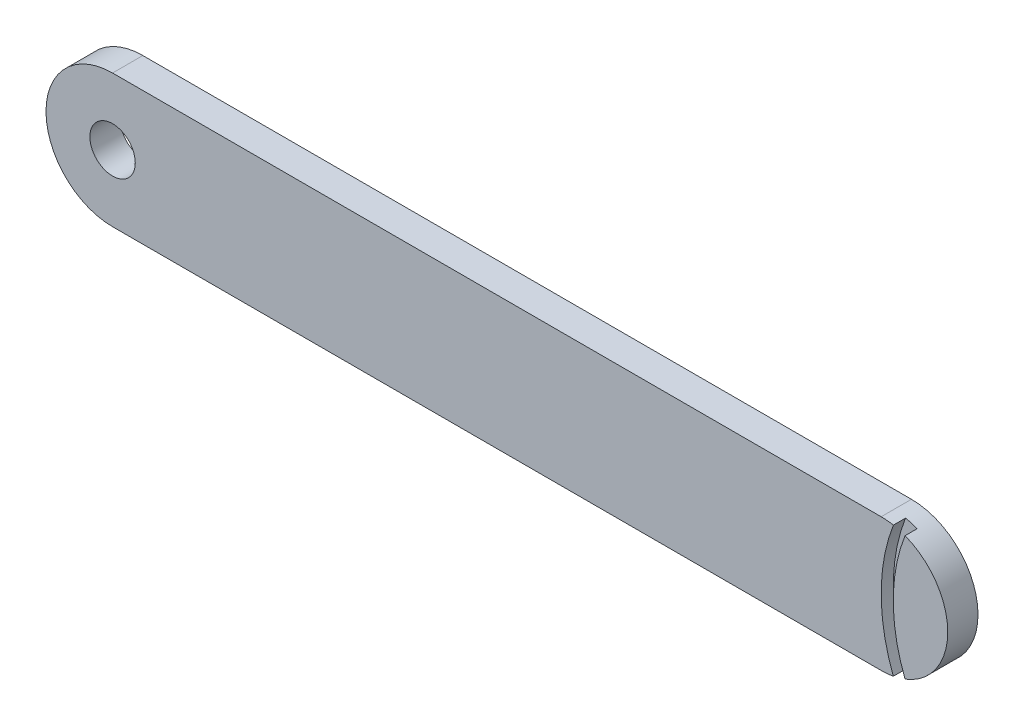
SolidWorks part; units mm, degrees
material "ABS"
ref_plane "Front Plane" through (0, 0, 0) normal (0, 0, 1) x (1, 0, 0)
ref_plane "Top Plane" through (0, 0, 0) normal (0, 1, 0) x (1, 0, 0)
ref_plane "Right Plane" through (0, 0, 0) normal (1, 0, 0) x (0, 0, -1)
sketch "Sketch1" plane through (0, 0, 0) normal (0, 0, 1) x (1, 0, 0)
  line L0 (0, 0) -> (127, 0)
  line L2 (127.1839, 22) -> (0, 22)
  arc A0 (127, 0) -> (127, 22) centre (127, 11) ccw
  arc A1 (0, 22) -> (0, 0) centre (0, 11) ccw
  circle A2 centre (0, 11) radius 3.75
  point P11 (0, 11)
  dimension "D3" = 7.5
  dimension "D1" = 127
  dimension "D2" = 22
extrude "Boss-Extrude1" add sketch "Sketch1" along normal blind 5
sketch "Sketch2" plane through (0, 0, 5) normal (0, 0, 1) x (1, 0, 0)
  arc A0 (129.0167, 21.8136) -> (129.0167, 0.1864) centre (157, 11) ccw
  arc A1 (127, 0) -> (127, 22) centre (127, 11) ccw construction
  arc A2 (130.95, 21.2663) -> (130.95, 0.7337) centre (157, 11) ccw
  arc A3 (129.0167, 0.1864) -> (130.95, 0.7337) centre (127, 11) ccw
  circle A4 centre (157, 11) radius 30 construction
  circle A5 centre (157, 11) radius 28 construction
  arc A6 (130.95, 21.2663) -> (129.0167, 21.8136) centre (127, 11) ccw
  point P0 (127, 11)
  point P6 (138, 11)
  dimension "D1" = 30
  dimension "D2" = 2
extrude "Cut-Extrude1" cut sketch "Sketch2" against normal blind 2
sketch "Sketch3" plane through (0, 0, 0) normal (0, 0, -1) x (-1, 0, 0)
  line L0 (0, 14.75) -> (-18.25, 14.75)
  line L1 (0, 7.25) -> (-18.25, 7.25)
  arc A0 (-18.25, 7.25) -> (-18.25, 14.75) centre (-18.25, 11) cw
  circle A1 centre (0, 11) radius 3.75 construction
  arc A5 (0, 14.75) -> (0, 7.25) centre (0, 11) ccw
  point P0 (0, 11)
  point P1 (-18.25, 11)
  point P6 (0, 14.75)
  point P7 (0, 7.25)
  point P22 (-22, 11)
  dimension "D1" = 22
extrude "Cut-Extrude2" cut sketch "Sketch3" against normal blind 1.5
